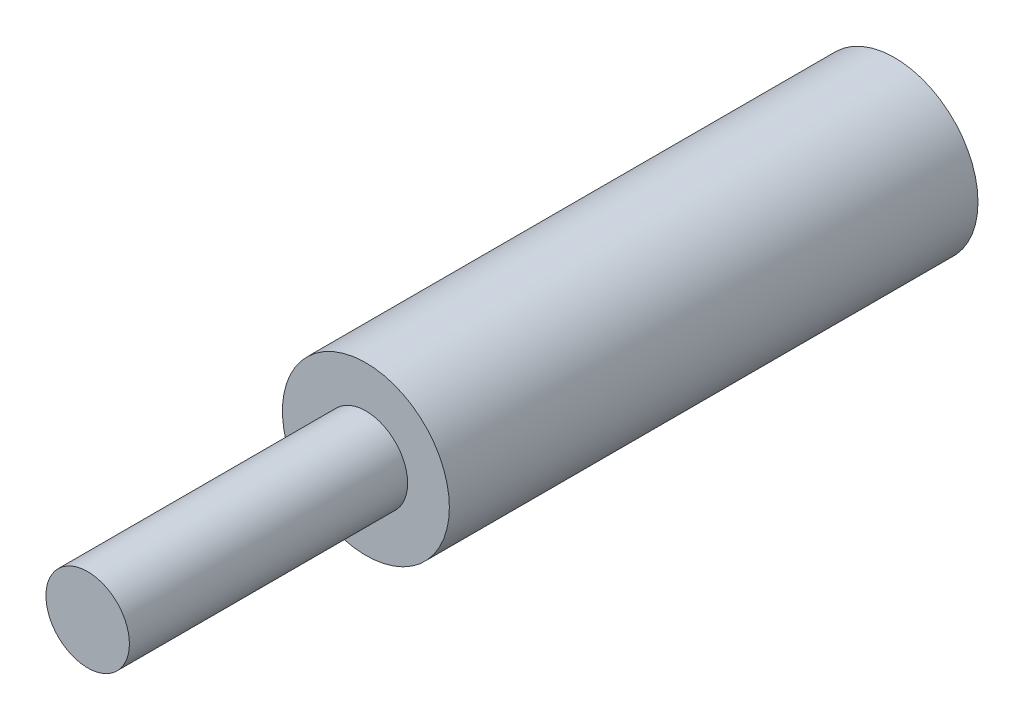
SolidWorks part; units mm, degrees
ref_plane "Alzado" through (0, 0, 0) normal (0, 0, 1) x (1, 0, 0)
ref_plane "Planta" through (0, 0, 0) normal (0, 1, 0) x (1, 0, 0)
ref_plane "Vista lateral" through (0, 0, 0) normal (1, 0, 0) x (0, 0, -1)
sketch "Croquis1" plane through (0, 0, 0) normal (0, 0, 1) x (1, 0, 0)
  circle A0 centre (0, 0) radius 3
  dimension "D1" = 6
extrude "Saliente-Extruir1" add sketch "Croquis1" along normal blind 19 contours A0
sketch "Croquis2" plane through (0, 0, 19) normal (0, 0, 1) x (1, 0, 0)
  circle A0 centre (0, 0) radius 1.5
  dimension "D1" = 3
extrude "Saliente-Extruir2" add sketch "Croquis2" along normal blind 10 contours A0
